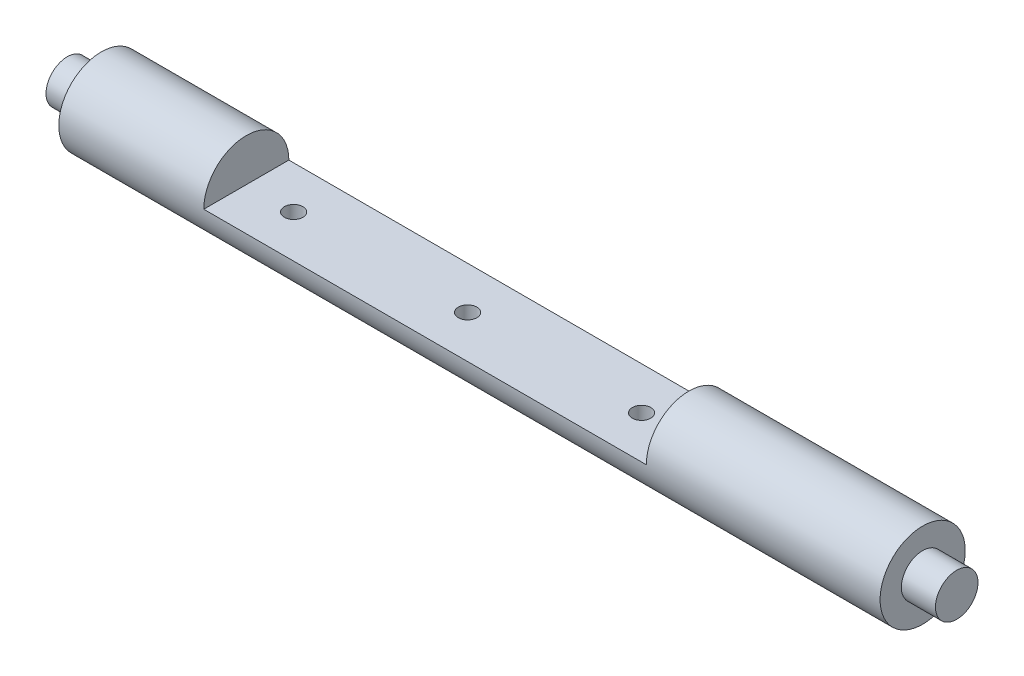
SolidWorks part; units mm, degrees
ref_plane "Front Plane" through (0, 0, 0) normal (0, 0, 1) x (1, 0, 0)
ref_plane "Top Plane" through (0, 0, 0) normal (0, 1, 0) x (1, 0, 0)
ref_plane "Right Plane" through (0, 0, 0) normal (1, 0, 0) x (0, 0, -1)
sketch "Sketch1" plane through (0, 0, 0) normal (1, 0, 0) x (0, 0, -1)
  circle A0 centre (0, 0) radius 7.9375
  dimension "D1" = 15.875
extrude "Boss-Extrude1" add sketch "Sketch1" along normal mid plane 153.162
sketch "Sketch2" plane through (0, 0, 0) normal (0, 1, 0) x (1, 0, 0)
  line L0 (-49.2919, 7.9375) -> (-49.2919, -25.0825) construction
  line L1 (32.9871, 12.7) -> (-49.5459, 12.7)
  line L2 (32.9871, 12.7) -> (32.9871, -12.7)
  line L3 (32.9871, -12.7) -> (-49.5459, -12.7)
  line L4 (-49.5459, 12.7) -> (-49.5459, -12.7)
  line L5 (32.9871, 12.7) -> (-49.5459, -12.7) construction
  line L6 (32.9871, -12.7) -> (-49.5459, 12.7) construction
  line L7 (32.7331, -25.0825) -> (32.7331, 7.9375) construction
  line L10 (32.7331, -25.0825) -> (32.7331, 7.9375) construction
  line L11 (-49.2919, 7.9375) -> (-49.2919, -25.0825) construction
  point P0 (-8.2794, 0)
  dimension "D1" = 25.4
  dimension "D2" = 0.254
  dimension "D3" = 0.254
sketch "Sketch3" plane through (-76.581, 0, 0) normal (-1, 0, 0) x (0, 0, 1)
  circle A0 centre (0, 0) radius 3.9688
  dimension "D1" = 7.9375
extrude "Boss-Extrude2" add sketch "Sketch3" along normal blind 6.35
sketch "Sketch4" plane through (76.581, 0, 0) normal (1, 0, 0) x (0, 0, -1)
  circle A0 centre (0, 0) radius 3.9688
  dimension "D1" = 7.9375
extrude "Boss-Extrude3" add sketch "Sketch4" along normal blind 6.35
extrude "Cut-Extrude1" cut sketch "Sketch2" along normal through all
sketch "Sketch5" plane through (0, 0, 0) normal (0, 1, 0) x (1, 0, 0)
  circle A0 centre (-40.7194, 0) radius 1.7272
  circle A1 centre (-8.2794, 0) radius 1.7272
  circle A2 centre (24.1606, 0) radius 1.7272
  circle A3 centre (24.1606, 0) radius 2.2225 construction
  circle A4 centre (-8.2794, 0) radius 2.2225 construction
  circle A5 centre (-40.7194, 0) radius 2.2225 construction
  point P10 (-8.2794, 0)
  point P13 (-8.927, -0.7978)
  dimension "D1" = 3.4544
extrude "Cut-Extrude2" cut sketch "Sketch5" against normal through all
